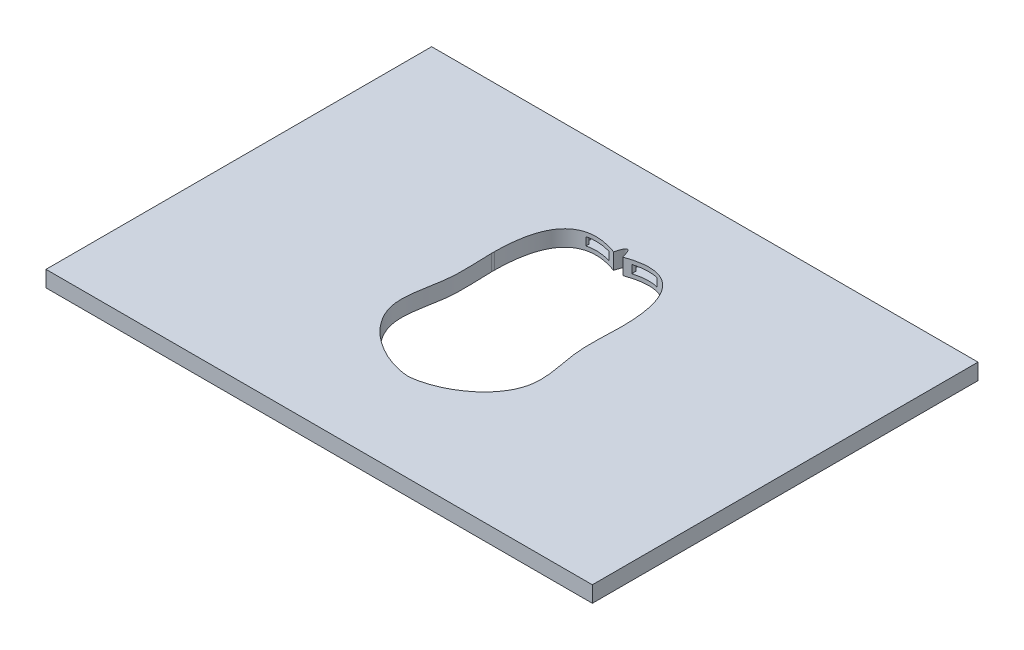
SolidWorks part; units mm, degrees
ref_plane "前视基准面" through (0, 0, 0) normal (0, 0, 1) x (1, 0, 0)
ref_plane "上视基准面" through (0, 0, 0) normal (0, 1, 0) x (1, 0, 0)
ref_plane "右视基准面" through (0, 0, 0) normal (1, 0, 0) x (0, 0, -1)
sketch "草图2" plane through (0, 0, 0) normal (0, 1, 0) x (1, 0, 0)
  line L1 (-17, 12) -> (17, 12)
  line L2 (-17, 12) -> (-17, -12)
  line L3 (-17, -12) -> (17, -12)
  line L4 (17, 12) -> (17, -12)
  line L5 (-17, 12) -> (17, -12) construction
  line L6 (-17, -12) -> (17, 12) construction
  point P0 (0, 0)
  dimension "D1" = 34
  dimension "D2" = 24
extrude "凸台-拉伸1" add sketch "草图2" along normal blind 1
sketch "草图3" plane through (0, 1, 0) normal (0, 1, 0) x (1, 0, 0)
  line L0 (0, 6.5) -> (0, -6.5)
  line L1 (-4, 6.5) -> (4, 6.5)
  line L2 (-4, 6.5) -> (-4, -6.5)
  line L3 (-4, -6.5) -> (4, -6.5)
  line L4 (4, 6.5) -> (4, -6.5)
  line L5 (-4, 6.5) -> (4, -6.5) construction
  line L6 (-4, -6.5) -> (4, 6.5) construction
  spline S0 degree 3 poles (0, 6.5) (-3.3774, 7.8914) (-4.2541, 3.9794) (-3.7737, -0.0755) (-5.1285, -4.0821) (-1.8115, -6.3831) (0, -6.5) knots 0 0 0 0 0.352467 0.509475 0.685816 0.974825 0.974825 0.974825 0.974825
  spline S1 degree 3 poles (0, 6.5) (3.3774, 7.8914) (4.2541, 3.9794) (3.7737, -0.0755) (5.1285, -4.0821) (1.8115, -6.3831) (0, -6.5) knots 0 0 0 0 0.352467 0.509475 0.685816 0.974825 0.974825 0.974825 0.974825
  spline S2 degree 2 poles (0.283, 6.6094) (-0.0025, 7.7527) (-0.2775, 6.6074) knots 0 0 0 1 1 1
  point P0 (0, 0)
  point P4 (0.0512, 0)
  dimension "D1" = 13
  dimension "D2" = 8
extrude "切除-拉伸2" cut sketch "草图3" against normal blind 1 contours S1 L1 L0 L4 | L1 S0 L2 L0 | S1 L4 | L2 S0 | L1 S0 | S1 L1 | S1 S2 S0
ref_plane "基准面1" through (0, 0, 8) normal (0, 0, 1) x (1, 0, 0)
sketch "草图4" plane through (0, 0, 8) normal (0, 0, 1) x (1, 0, 0)
  line L0 (0, 0) -> (0, 0.5)
  line L2 (-1, 0.25) -> (1, 0.25)
  line L3 (-1, 0.25) -> (-1, 0.75)
  line L4 (-1, 0.75) -> (1, 0.75)
  line L5 (1, 0.25) -> (1, 0.75)
  line L6 (-1, 0.25) -> (1, 0.75) construction
  line L7 (-1, 0.75) -> (1, 0.25) construction
  dimension "D1" = 0.5
  dimension "D2" = 0.5
  dimension "D3" = 2
extrude "切除-拉伸3" cut sketch "草图4" against normal blind 3
ref_plane "基准面2" through (0, 0, -8) normal (0, 0, -1) x (-1, 0, 0)
sketch "草图5" plane through (0, 0, -8) normal (0, 0, -1) x (-1, 0, 0)
  line L0 (0, 0) -> (0, 0.5)
  line L1 (0, 0.5) -> (-1.4581, 0.5)
  line L2 (0.7081, 0.75) -> (0.7081, 0.25)
  line L3 (-0.7081, 0.75) -> (-2.2081, 0.75)
  line L4 (-0.7081, 0.75) -> (-0.7081, 0.25)
  line L5 (-0.7081, 0.25) -> (-2.2081, 0.25)
  line L6 (-2.2081, 0.75) -> (-2.2081, 0.25)
  line L7 (-0.7081, 0.75) -> (-2.2081, 0.25) construction
  line L8 (-0.7081, 0.25) -> (-2.2081, 0.75) construction
  line L9 (0.7081, 0.75) -> (2.2081, 0.75)
  line L10 (2.2081, 0.75) -> (2.2081, 0.25)
  line L11 (0.7081, 0.25) -> (2.2081, 0.25)
  dimension "D1" = 0.5
  dimension "D2" = 1.5
  dimension "D3" = 0.5
extrude "切除-拉伸4" cut sketch "草图5" against normal blind 3
sketch "草图6" plane through (0, 0, 8) normal (0, 0, -1) x (-1, 0, 0)
  line L0 (1, 0.75) -> (-1, 0.25)
  line L2 (1.2, 0.75) -> (-1.2, 0.75)
  line L3 (1.2, 0.75) -> (1.2, 0.25)
  line L4 (1.2, 0.25) -> (-1.2, 0.25)
  line L5 (-1.2, 0.75) -> (-1.2, 0.25)
  line L6 (1.2, 0.75) -> (-1.2, 0.25) construction
  line L7 (1.2, 0.25) -> (-1.2, 0.75) construction
  point P4 (0, 0.5)
  line M1 (-1, 0.25) -> (1, 0.25)
  line M2 (1, 0.25) -> (1, 0.75)
  line M3 (1, 0.75) -> (-1, 0.75)
  line M4 (-1, 0.75) -> (-1, 0.25)
  dimension "D1" = 0.5
  dimension "D2" = 2.4
extrude "切除-拉伸6" cut sketch "草图6" along normal blind 1.2 contours L4 L3 L2 M2 | L0 M2 M1 | L0 M3 M4 | L2 L5 L4 M4
sketch "草图7" plane through (0, 0, -8) normal (0, 0, 1) x (1, 0, 0)
  line L0 (-0.7081, 0.25) -> (-2.2081, 0.75)
  line L2 (-2.4081, 0.25) -> (-0.5081, 0.25)
  line L3 (-2.4081, 0.25) -> (-2.4081, 0.75)
  line L4 (-2.4081, 0.75) -> (-0.5081, 0.75)
  line L5 (-0.5081, 0.25) -> (-0.5081, 0.75)
  line L6 (-2.4081, 0.25) -> (-0.5081, 0.75) construction
  line L7 (-2.4081, 0.75) -> (-0.5081, 0.25) construction
  point P4 (-1.4581, 0.5)
  line M1 (-0.7081, 0.25) -> (-0.7081, 0.75)
  line M2 (-0.7081, 0.75) -> (-2.2081, 0.75)
  line M3 (-2.2081, 0.75) -> (-2.2081, 0.25)
  line M4 (-2.2081, 0.25) -> (-0.7081, 0.25)
  dimension "D1" = 0.5
  dimension "D2" = 1.9
extrude "切除-拉伸7" cut sketch "草图7" along normal blind 1 contours L0 M4 M3 | L4 L3 L2 M3 | L0 M1 M2 | L2 L5 L4 M1
pattern_linear "阵列(线性)1" count 2 spacing 2.917 along (1, 0, 0) of "切除-拉伸7"
